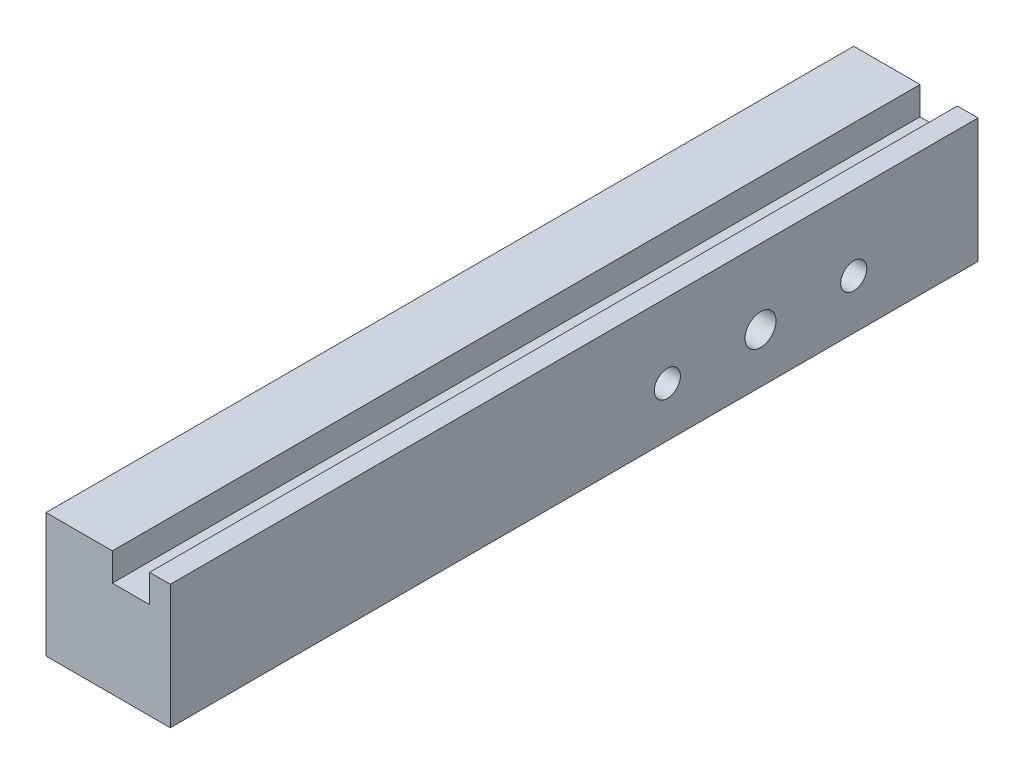
SolidWorks part; units mm, degrees
ref_plane "前视基准面" through (0, 0, 0) normal (0, 0, 1) x (1, 0, 0)
ref_plane "上视基准面" through (0, 0, 0) normal (0, 1, 0) x (1, 0, 0)
ref_plane "右视基准面" through (0, 0, 0) normal (1, 0, 0) x (0, 0, -1)
sketch "草图1" plane through (0, 0, 0) normal (0, 0, 1) x (1, 0, 0)
  line L1 (0, 0) -> (20, 0)
  line L2 (0, 0) -> (0, 20)
  line L3 (0, 20) -> (20, 20)
  line L4 (20, 0) -> (20, 20)
  dimension "D1" = 20
  dimension "D2" = 20
extrude "凸台-拉伸1" add sketch "草图1" along normal blind 130
sketch "草图2" plane through (0, 20, 0) normal (0, 1, 0) x (1, 0, 0)
  line L0 (20, 0) -> (0, 0) construction
  line L1 (10.6754, 0) -> (16.6716, 0)
  line L2 (10.6754, 0) -> (10.6754, -130)
  line L3 (10.6754, -130) -> (16.6716, -130)
  line L4 (16.6716, 0) -> (16.6716, -130)
  line L5 (20, -130) -> (0, -130) construction
extrude "切除-拉伸1" cut sketch "草图2" against normal blind 4.5
hole_wizard "M5 螺纹孔1" positions "草图3" profile "草图4" tap size "M5" standard "ISO" end condition through all
sketch "草图3" plane through (0, 0, 0) normal (-1, 0, 0) x (0, 0, 1)
  line L0 (130, 0) -> (0, 0) construction
  line L3 (0, 20) -> (0, 0) construction
  point P0 (20, 8)
  point P2 (50, 8)
  dimension "D1" = 30
  dimension "D2" = 8
  dimension "D3" = 20
sketch "草图4" plane through (0, 8, 20) normal (0, 1, 0) x (0, 0, 1)
  line L0 (0, 0) -> (0, 20)
  line L1 (0, 20) -> (2.1, 20)
  line L2 (2.1, 20) -> (2.1, 0)
  line L5 (2.1, 0) -> (0, 0)
  line L11 (0, -6.35) -> (0, 107.95) construction
  dimension "通孔螺纹孔钻头直径" = 4.2
  dimension "通孔螺纹孔钻头深度" = 20
cosmetic thread "孔螺蚊线1" parameters "D2"=5
cosmetic thread "孔螺蚊线2" parameters "D2"=5
sketch "草图5" plane through (20, 0, 0) normal (1, 0, 0) x (0, 0, -1)
  circle A0 centre (-35, 8) radius 2.5
extrude "切除-拉伸2" cut sketch "草图5" against normal through all
